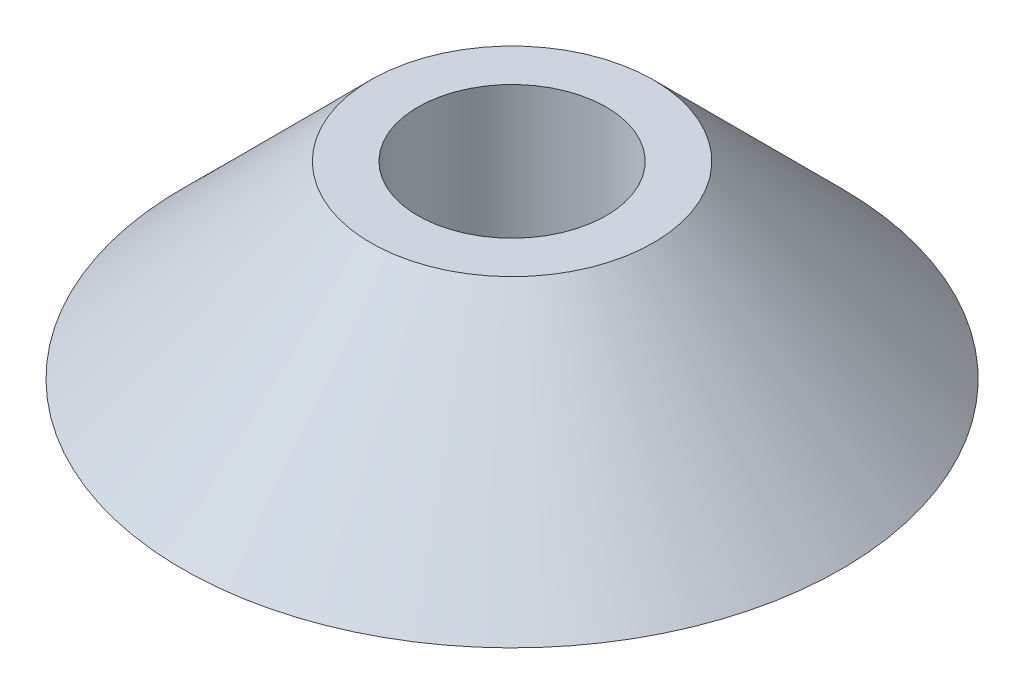
SolidWorks part; units mm, degrees
ref_plane "Front Plane" through (0, 0, 0) normal (0, 0, 1) x (1, 0, 0)
ref_plane "Top Plane" through (0, 0, 0) normal (0, 1, 0) x (1, 0, 0)
ref_plane "Right Plane" through (0, 0, 0) normal (1, 0, 0) x (0, 0, -1)
sketch "Sketch1" plane through (0, 0, 0) normal (0, 0, 1) x (1, 0, 0)
  line L0 (0, -1000.6938) -> (0, 48999.3062) construction
  line L1 (6.35, 0) -> (22.225, 0)
  line L2 (22.225, 0) -> (9.525, 12.7)
  line L3 (9.525, 12.7) -> (6.35, 12.7)
  line L4 (6.35, 12.7) -> (0, 12.7) construction
  line L5 (6.35, 12.7) -> (6.35, 0)
  line L6 (0, 0) -> (6.35, 0) construction
  dimension "D1" = 45
  dimension "D2" = 12.7
  dimension "D3" = 9.525
  dimension "D4" = 12.7
revolve "Revolve1" add sketch "Sketch1" angle 360 about L0
